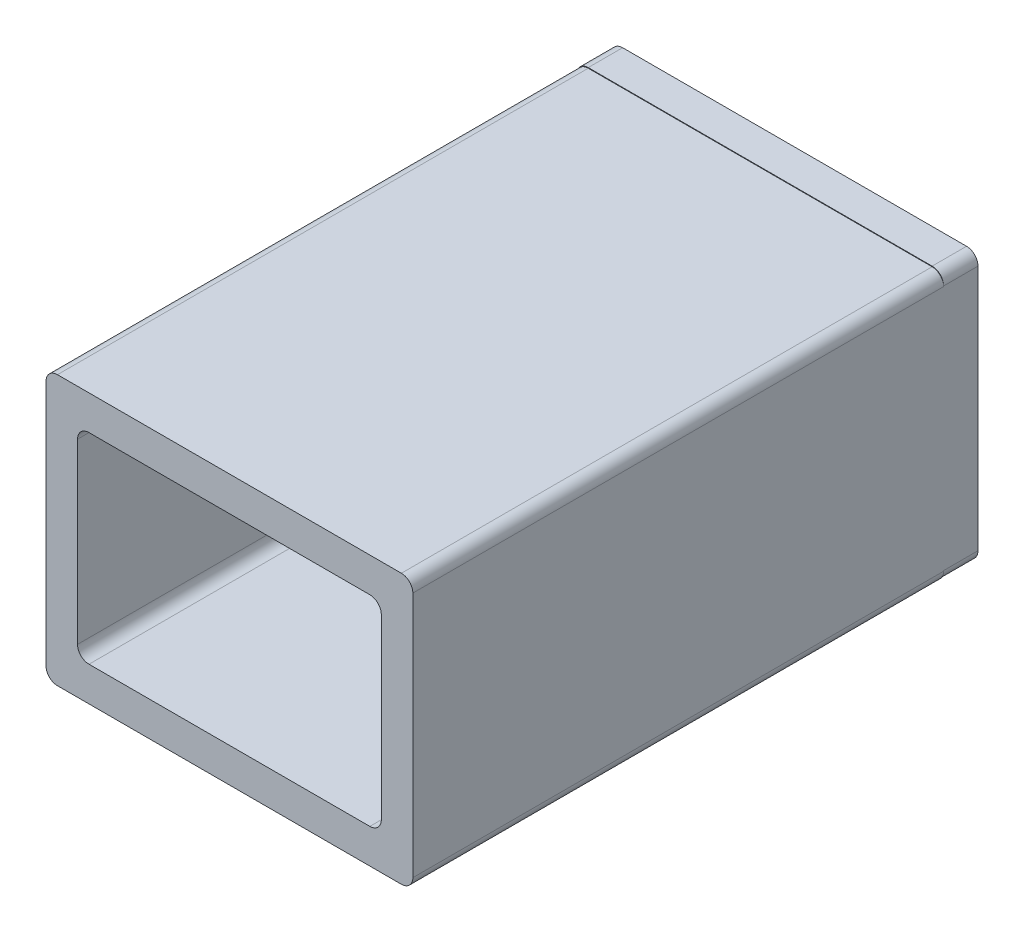
SolidWorks part; units mm, degrees
ref_plane "Front Plane" through (0, 0, 0) normal (0, 0, 1) x (1, 0, 0)
ref_plane "Top Plane" through (0, 0, 0) normal (0, 1, 0) x (1, 0, 0)
ref_plane "Right Plane" through (0, 0, 0) normal (1, 0, 0) x (0, 0, -1)
sketch "Sketch1" plane through (0, 0, 0) normal (0, 0, 1) x (1, 0, 0)
  line L1 (-12.25, 8.75) -> (12.25, 8.75)
  line L2 (-13.25, 7.75) -> (-13.25, -7.75)
  line L3 (-12.25, -8.75) -> (12.25, -8.75)
  line L4 (13.25, 7.75) -> (13.25, -7.75)
  line L5 (-13.25, 8.75) -> (13.25, -8.75) construction
  line L6 (-13.25, -8.75) -> (13.25, 8.75) construction
  line L7 (-15, 11.75) -> (15, 11.75)
  line L8 (-16, 10.75) -> (-16, -10.75)
  line L9 (-15, -11.75) -> (15, -11.75)
  line L10 (16, 10.75) -> (16, -10.75)
  line L11 (-16, 11.75) -> (16, -11.75) construction
  line L12 (-16, -11.75) -> (16, 11.75) construction
  arc A0 (-12.25, 8.75) -> (-13.25, 7.75) centre (-12.25, 7.75) ccw
  arc A1 (12.25, 8.75) -> (13.25, 7.75) centre (12.25, 7.75) cw
  arc A2 (12.25, -8.75) -> (13.25, -7.75) centre (12.25, -7.75) ccw
  arc A3 (-13.25, -7.75) -> (-12.25, -8.75) centre (-12.25, -7.75) ccw
  arc A4 (15, -11.75) -> (16, -10.75) centre (15, -10.75) ccw
  arc A5 (15, 11.75) -> (16, 10.75) centre (15, 10.75) cw
  arc A6 (-15, 11.75) -> (-16, 10.75) centre (-15, 10.75) ccw
  arc A7 (-16, -10.75) -> (-15, -11.75) centre (-15, -10.75) ccw
  point P0 (0, 0)
  point P18 (0, 0)
  dimension "D3" = 1
  dimension "D6" = 1
  dimension "D1" = 17.5
  dimension "D2" = 26.5
  dimension "D4" = 32
  dimension "D5" = 23.5
extrude "Boss-Extrude1" add sketch "Sketch1" along normal blind 46.3
sketch "Sketch3" plane through (0, 0, 0) normal (0, 0, 1) x (1, 0, 0)
  line L0 (15.6606, -11.4507) -> (16, -11.7) construction
  line L7 (-15, 11.8) -> (15, 11.8)
  line L8 (-16, 10.8) -> (-16, -10.7)
  line L9 (-15, -11.7) -> (15, -11.7)
  line L10 (16, 10.8) -> (16, -10.7)
  line L11 (-16, 11.8) -> (-15.6606, 11.5507) construction
  line L12 (-16, -11.7) -> (-15.6606, -11.4507) construction
  line L14 (15.6606, 11.5507) -> (16, 11.8) construction
  arc A4 (15, -11.7) -> (16, -10.7) centre (15, -10.7) ccw
  arc A5 (15, 11.8) -> (16, 10.8) centre (15, 10.8) cw
  arc A6 (-15, 11.8) -> (-16, 10.8) centre (-15, 10.8) ccw
  arc A7 (-16, -10.7) -> (-15, -11.7) centre (-15, -10.7) ccw
  point P0 (0, 0)
  point P18 (0, 0.05)
  dimension "D6" = 1
  dimension "D4" = 32
  dimension "D5" = 23.5
extrude "Boss-Extrude2" add sketch "Sketch3" against normal blind 3
